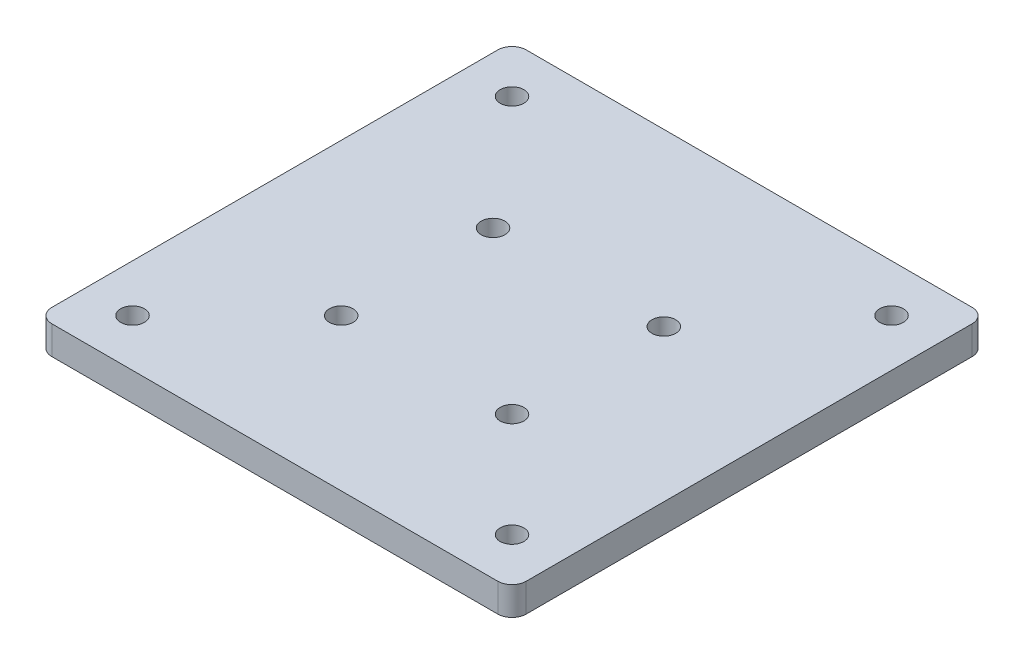
SolidWorks part; units mm, degrees
ref_plane "Front Plane" through (0, 0, 0) normal (0, 0, 1) x (1, 0, 0)
ref_plane "Top Plane" through (0, 0, 0) normal (0, 1, 0) x (1, 0, 0)
ref_plane "Right Plane" through (0, 0, 0) normal (1, 0, 0) x (0, 0, -1)
sketch "Sketch1" plane through (0, 0, 0) normal (0, 1, 0) x (1, 0, 0)
  line L1 (-10, 90) -> (90, 90)
  line L2 (-10, 90) -> (-10, -10)
  line L3 (-10, -10) -> (90, -10)
  line L4 (90, 90) -> (90, -10)
  circle A0 centre (0, 0) radius 2.5
  circle A1 centre (80, 0) radius 2.5
  circle A2 centre (0, 80) radius 2.5
  circle A3 centre (80, 80) radius 2.5
  circle A4 centre (0, 32) radius 2.5 [skipped]
  circle A5 centre (80, 32) radius 2.5 [skipped]
  circle A6 centre (22, 22) radius 2.5
  circle A7 centre (58, 22) radius 2.5
  circle A8 centre (22, 54) radius 2.5
  circle A9 centre (58, 54) radius 2.5
  dimension "D1" = 5
  dimension "D9" = 5
  dimension "D10" = 5
  dimension "D12" = 10
  dimension "D13" = 100
  dimension "D14" = 10
  dimension "D15" = 5
  dimension "D16" = 5
  dimension "D17" = 5
  dimension "D18" = 5
  dimension "D22" = 36
  dimension "D21" = 32
  dimension "D23" = 32
  dimension "D24" = 32
  dimension "D8" = 90
  dimension "D11" = 90
  dimension "D4" = 10
  dimension "D5" = 10
  dimension "D6" = 10
  dimension "D7" = 100
  dimension "D19" = 32
  dimension "D20" = 36
  dimension "D2" = 2
  dimension "D3" = 2
extrude "Boss-Extrude1" add sketch "Sketch1" along normal blind 6
fillet "Fillet1" radius 3 2 edges at (-10, 3, 10) (90, 3, 10)
fillet "Fillet2" radius 3 2 edges at (-10, 3, -90) (90, 3, -90)
scale "Scale1" scale about centroid uniform scaling yes scale factor 7.5
